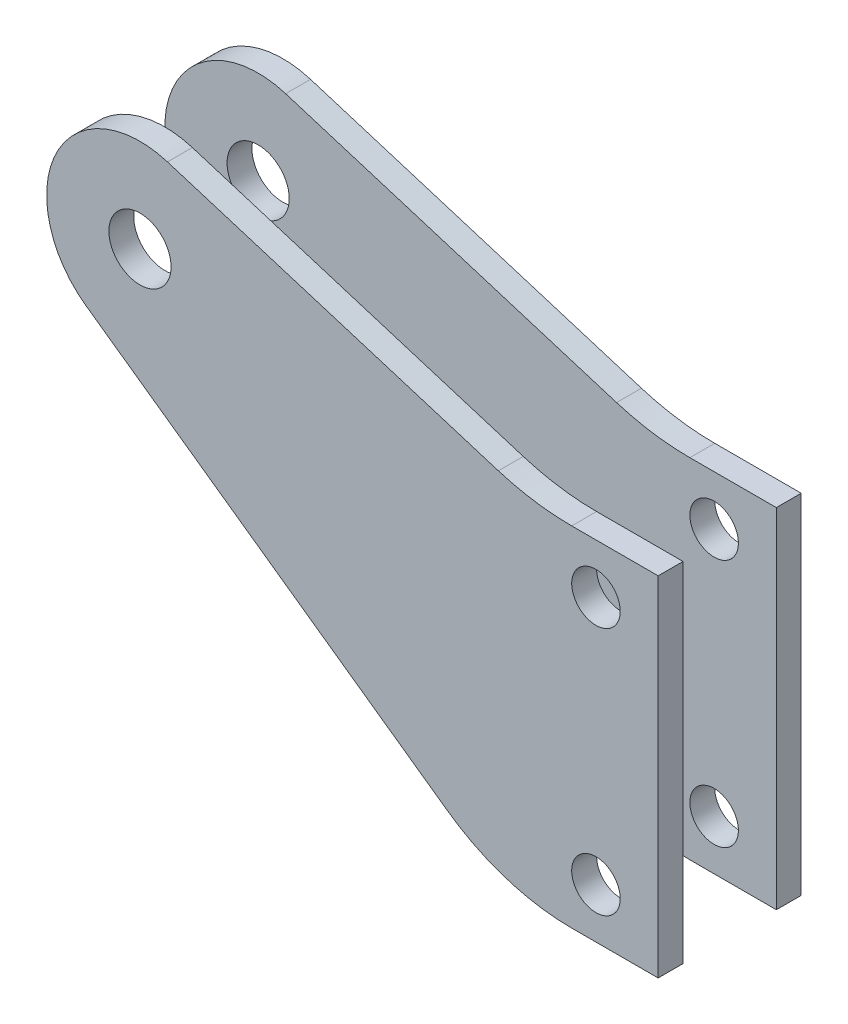
SolidWorks part; units mm, degrees
material "6061-T6 (SS)"
ref_plane "Front Plane" through (0, 0, 0) normal (0, 0, 1) x (1, 0, 0)
ref_plane "Top Plane" through (0, 0, 0) normal (0, 1, 0) x (1, 0, 0)
ref_plane "Right Plane" through (0, 0, 0) normal (1, 0, 0) x (0, 0, -1)
sketch "Sketch1" plane through (0, 0, 0) normal (0, 0, 1) x (1, 0, 0)
  line L0 (2.8069, 9.102) -> (36.5924, -1.3167)
  line L1 (52.9039, -2.4446) -> (52.9039, -38.0046)
  line L2 (52.9039, -38.0046) -> (44.0774, -38.0046)
  line L3 (46.5539, -7.5246) -> (46.5539, -32.9246) construction
  line L4 (-5.5136, -7.767) -> (31.3774, -33.9551)
  line L5 (44.0774, -2.4446) -> (52.9039, -2.4446)
  line L6 (44.0774, -7.5246) -> (44.0774, -2.4446) construction
  circle A0 centre (46.5539, -7.5246) radius 2.4765
  circle A1 centre (46.5539, -32.9246) radius 2.4765
  circle A2 centre (0, 0) radius 3.175
  arc A3 (2.8069, 9.102) -> (-5.5136, -7.767) centre (0, 0) ccw
  arc A4 (44.0774, -2.4446) -> (36.5924, -1.3167) centre (44.0774, 22.9554) cw
  arc A5 (44.0774, -38.0046) -> (31.3774, -33.9551) centre (44.0774, -16.0647) cw
  point P2 (52.9039, -20.2246)
  point P11 (46.5539, -20.2246)
  dimension "D1" = 4.953
  dimension "D7" = 6.35
  dimension "D8" = 6.35
  dimension "D9" = 12.7
  dimension "D10" = 25.4
  dimension "D2" = 25.4
  dimension "D3" = 7.5246
  dimension "D4" = 46.5539
  dimension "D5" = 5.08
  dimension "D6" = 6.35
extrude "Steering Arm" add sketch "Sketch1" along normal blind 2.54 from offset 4.7625
mirror "Steering Arm Mirror" about plane through (0, 0, 0) normal (0, 0, 1) of bodies 101
